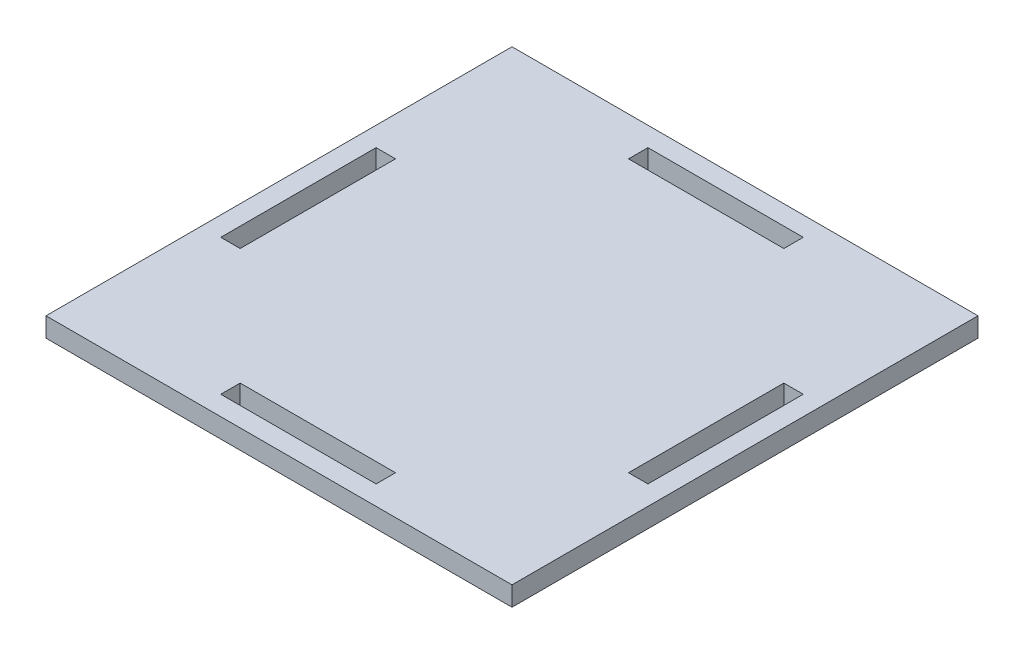
SolidWorks part; units mm, degrees
ref_plane "Front Plane" through (0, 0, 0) normal (0, 0, 1) x (1, 0, 0)
ref_plane "Top Plane" through (0, 0, 0) normal (0, 1, 0) x (1, 0, 0)
ref_plane "Right Plane" through (0, 0, 0) normal (1, 0, 0) x (0, 0, -1)
sketch "Sketch1" plane through (0, 0, 0) normal (0, 1, 0) x (1, 0, 0)
  line L0 (0, 0) -> (0, 152.4)
  line L1 (0, 152.4) -> (152.4, 152.4)
  line L2 (0, 0) -> (152.4, 0)
  line L3 (152.4, 0) -> (152.4, 152.4)
  dimension "D1" = 152.4
  dimension "D2" = 152.4
extrude "Boss-Extrude1" add sketch "Sketch1" along normal blind 6.35
sketch "Sketch2" plane through (0, 6.35, 0) normal (0, 1, 0) x (1, 0, 0)
  line L0 (76.2, 152.4) -> (76.2, 0) construction
  line L1 (152.4, 152.4) -> (0, 152.4) construction
  line L2 (0, 0) -> (152.4, 0) construction
  line L3 (0, 76.2) -> (152.4, 76.2) construction
  line L4 (0, 152.4) -> (0, 0) construction
  line L5 (152.4, 0) -> (152.4, 152.4) construction
  line L6 (9.525, 101.6) -> (9.525, 152.4) construction
  line L7 (6.35, 101.6) -> (12.7, 101.6)
  line L8 (6.35, 101.6) -> (6.35, 50.8)
  line L9 (6.35, 50.8) -> (12.7, 50.8)
  line L10 (12.7, 101.6) -> (12.7, 50.8)
  line L11 (9.525, 50.8) -> (9.525, 0) construction
  line L12 (146.05, 101.6) -> (139.7, 101.6)
  line L13 (146.05, 50.8) -> (139.7, 50.8)
  line L14 (146.05, 101.6) -> (146.05, 50.8)
  line L15 (139.7, 101.6) -> (139.7, 50.8)
  line L16 (50.8, 9.525) -> (0, 9.525) construction
  line L17 (50.8, 6.35) -> (101.6, 6.35)
  line L18 (50.8, 6.35) -> (50.8, 12.7)
  line L19 (50.8, 12.7) -> (101.6, 12.7)
  line L20 (101.6, 6.35) -> (101.6, 12.7)
  line L21 (101.6, 9.525) -> (152.4, 9.525) construction
  line L22 (101.6, 146.05) -> (101.6, 139.7)
  line L23 (50.8, 146.05) -> (50.8, 139.7)
  line L24 (50.8, 139.7) -> (101.6, 139.7)
  line L25 (50.8, 146.05) -> (101.6, 146.05)
  dimension "D1" = 50.8
  dimension "D2" = 6.35
  dimension "D3" = 6.35
  dimension "D4" = 6.35
  dimension "D5" = 6.35
  dimension "D6" = 50.8
extrude "Cut-Extrude1" cut sketch "Sketch2" against normal blind 16.51 and the other way blind 6.35
sketch "Sketch3" plane through (0, 6.35, 0) normal (0, 1, 0) x (1, 0, 0)
  line L0 (76.2, 152.4) -> (76.2, 0) construction
  line L1 (152.4, 152.4) -> (0, 152.4) construction
  line L2 (0, 0) -> (152.4, 0) construction
  line L3 (0, 76.2) -> (152.4, 76.2) construction
  line L4 (0, 152.4) -> (0, 0) construction
  line L5 (152.4, 0) -> (152.4, 152.4) construction
  line L7 (139.7, 12.7) -> (12.7, 12.7)
  line L8 (139.7, 12.7) -> (139.7, 139.7)
  line L9 (139.7, 139.7) -> (12.7, 139.7)
  line L10 (12.7, 12.7) -> (12.7, 139.7)
  line L11 (139.7, 12.7) -> (12.7, 139.7) construction
  line L12 (139.7, 139.7) -> (12.7, 12.7) construction
  point P12 (76.2, 76.2)
  dimension "D1" = 127
  dimension "D2" = 127
